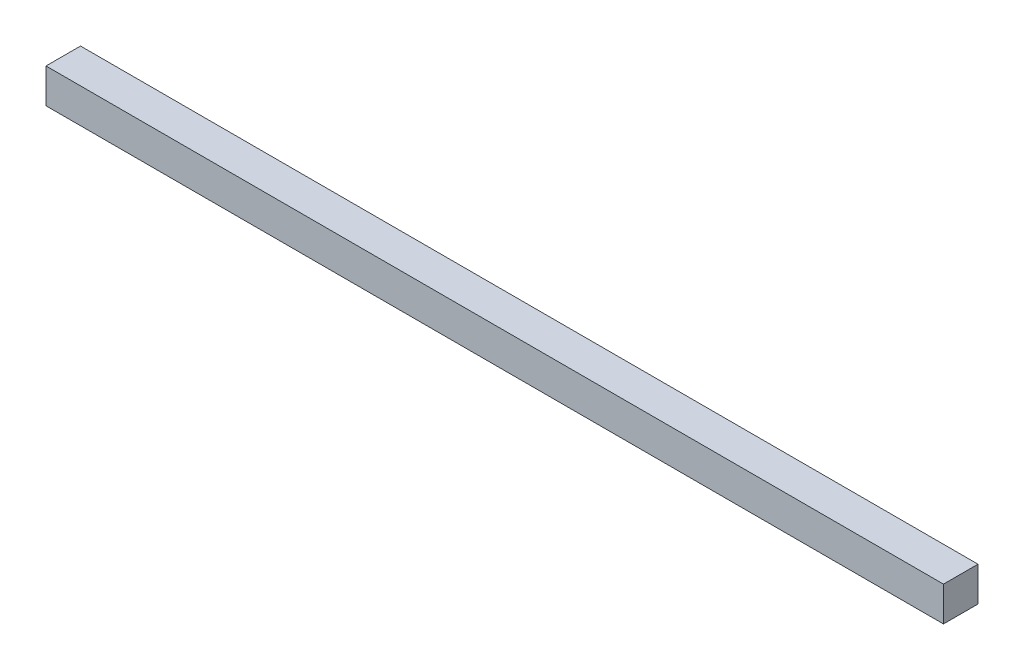
SolidWorks part; units mm, degrees
ref_plane "Front Plane" through (0, 0, 0) normal (0, 0, 1) x (1, 0, 0)
ref_plane "Top Plane" through (0, 0, 0) normal (0, 1, 0) x (1, 0, 0)
ref_plane "Right Plane" through (0, 0, 0) normal (1, 0, 0) x (0, 0, -1)
sketch "Sketch1" plane through (0, 0, 0) normal (0, 1, 0) x (1, 0, 0)
  line L0 (-130, 5) -> (130, -5) construction
  line L1 (-130, 5) -> (130, 5)
  line L2 (-130, 5) -> (-130, -5)
  line L3 (-130, -5) -> (130, -5)
  line L4 (130, 5) -> (130, -5)
  dimension "D1" = 260
  dimension "D2" = 10
extrude "Boss-Extrude1" add sketch "Sketch1" along normal blind 10
